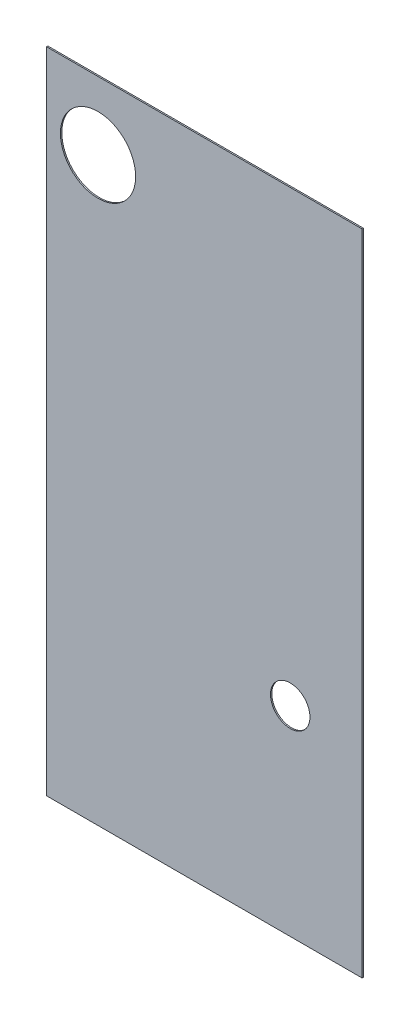
SolidWorks part; units mm, degrees
ref_plane "Front Plane" through (0, 0, 0) normal (0, 0, 1) x (1, 0, 0)
ref_plane "Top Plane" through (0, 0, 0) normal (0, 1, 0) x (1, 0, 0)
ref_plane "Right Plane" through (0, 0, 0) normal (1, 0, 0) x (0, 0, -1)
sketch "Sketch1" plane through (0, 0, 0) normal (0, 0, 1) x (1, 0, 0)
  line L1 (-13.7389, 1442.5417) -> (-618.8218, 1442.5417)
  line L2 (-13.7389, 1442.5417) -> (-13.7389, 198.5979)
  line L3 (-13.7389, 198.5979) -> (-618.8218, 198.5979)
  line L4 (-618.8218, 1442.5417) -> (-618.8218, 198.5979)
extrude "Boss-Extrude1" add sketch "Sketch1" along normal blind 2.54
sketch "Sketch3" plane through (0, 0, 2.54) normal (0, 0, 1) x (1, 0, 0)
  circle A0 centre (-520.1262, 1312.2267) radius 72.0725
  circle A1 centre (-151.6015, 581.8174) radius 37.8543
  point P4 (-520.1262, 1312.2267)
extrude "Cut-Extrude1" cut sketch "Sketch3" against normal through all both and the other way through all
sketch "Sketch4" plane through (0, 0, 2.54) normal (0, 0, 1) x (1, 0, 0)
  line L0 (-536.2036, 1128.7866) -> (-203.537, 1128.7866) construction
